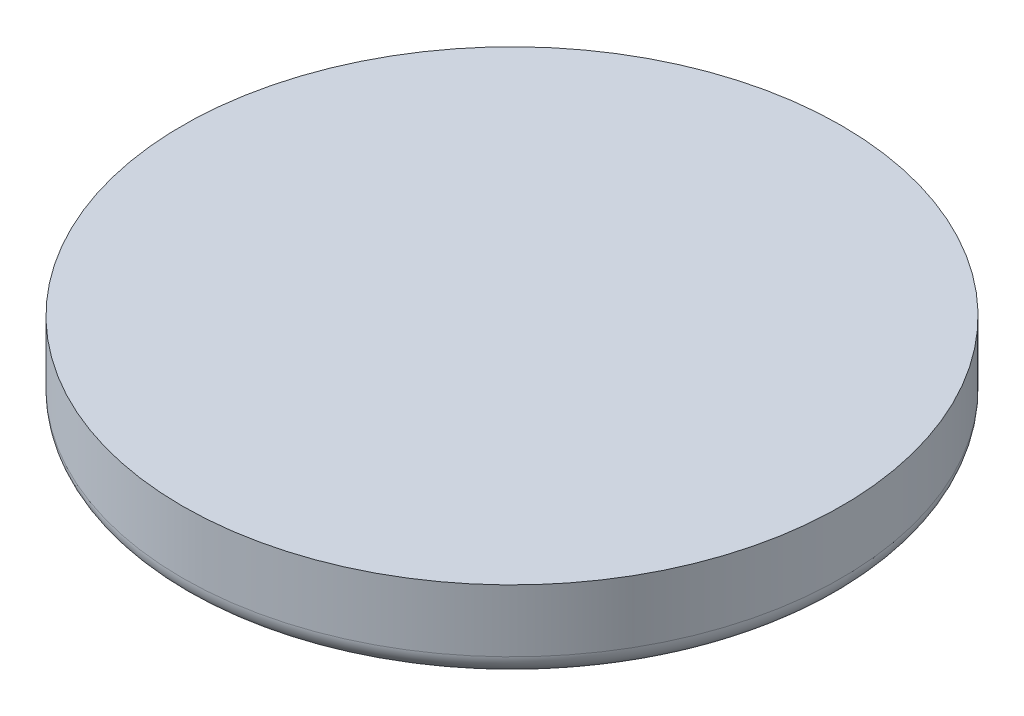
SolidWorks part; units mm, degrees
ref_plane "Front Plane" through (0, 0, 0) normal (0, 0, 1) x (1, 0, 0)
ref_plane "Top Plane" through (0, 0, 0) normal (0, 1, 0) x (1, 0, 0)
ref_plane "Right Plane" through (0, 0, 0) normal (1, 0, 0) x (0, 0, -1)
sketch "Sketch1" plane through (0, 0, 0) normal (0, 1, 0) x (1, 0, 0)
  circle A2 centre (0, 0) radius 3.175
  dimension "D1" = 6.35
extrude "Boss-Extrude1" add sketch "Sketch1" along normal blind 0.8
fillet "Fillet3" radius 0.2 1 edges at (0, 0, 3.175)
